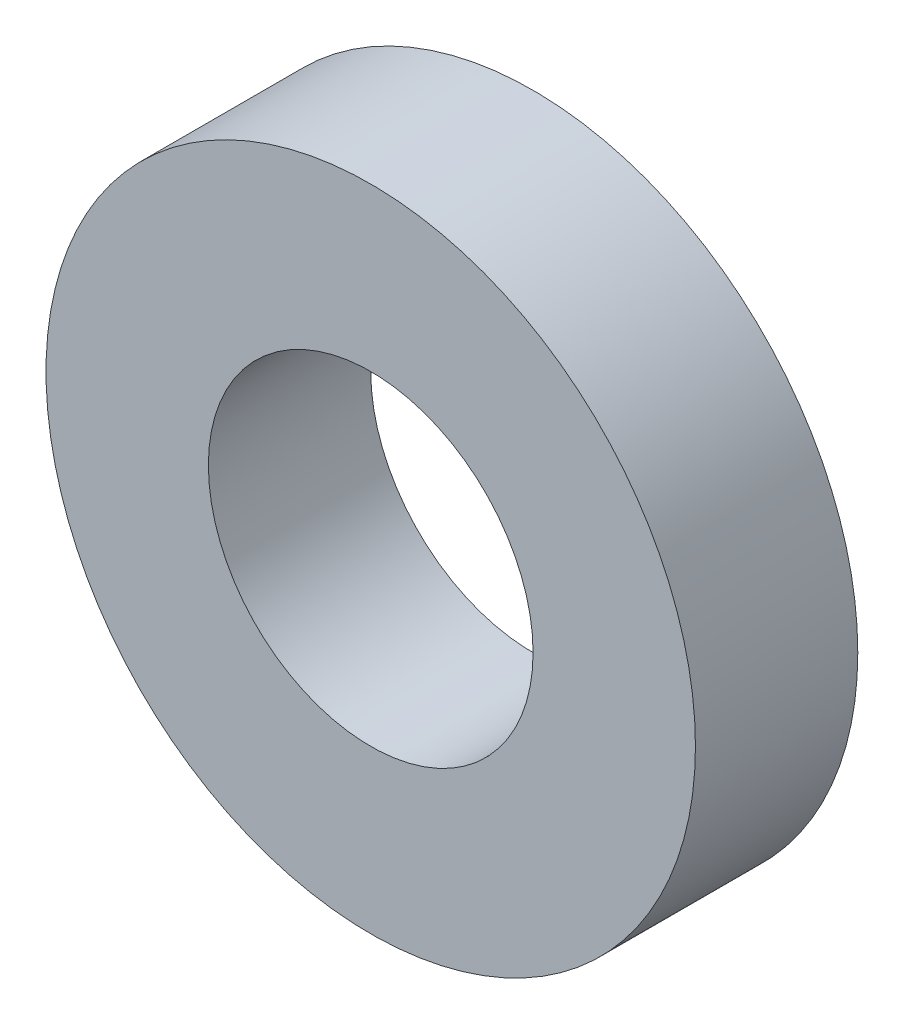
SolidWorks part; units mm, degrees
ref_plane "前视基准面" through (0, 0, 0) normal (0, 0, 1) x (1, 0, 0)
ref_plane "上视基准面" through (0, 0, 0) normal (0, 1, 0) x (1, 0, 0)
ref_plane "右视基准面" through (0, 0, 0) normal (1, 0, 0) x (0, 0, -1)
sketch "草图2" plane through (0, 0, 0) normal (0, 0, 1) x (1, 0, 0)
  circle A0 centre (0, 0) radius 3
  circle A1 centre (0, 0) radius 6
  dimension "D1" = 12
  dimension "D2" = 6
extrude "凸台-拉伸1" add sketch "草图2" along normal blind 3
